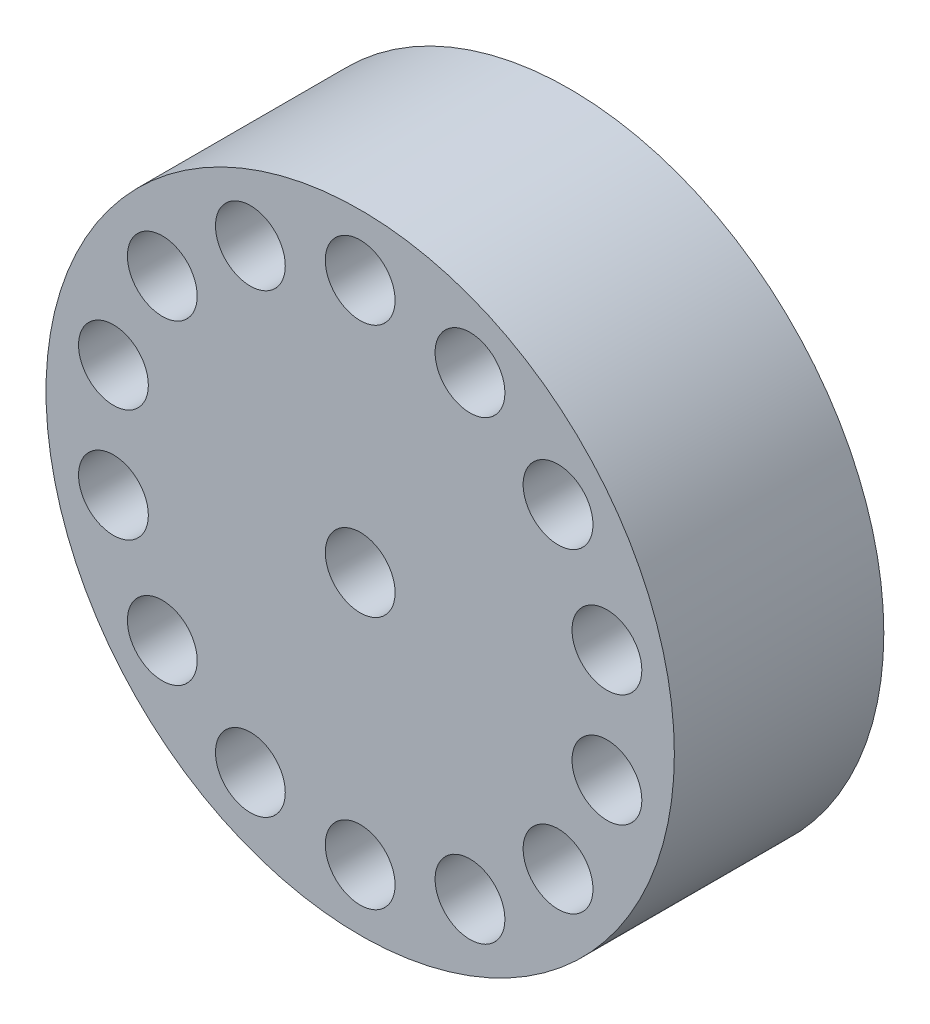
SolidWorks part; units mm, degrees
ref_plane "Płaszczyzna przednia" through (0, 0, 0) normal (0, 0, 1) x (1, 0, 0)
ref_plane "Płaszczyzna górna" through (0, 0, 0) normal (0, 1, 0) x (1, 0, 0)
ref_plane "Płaszczyzna prawa" through (0, 0, 0) normal (1, 0, 0) x (0, 0, -1)
sketch "Szkic1" plane through (0, 0, 0) normal (0, 0, 1) x (1, 0, 0)
  circle A0 centre (0, 0) radius 4.5
  circle A1 centre (0, 0) radius 0.5
extrude "Dodanie-wyciągnięcie1" add sketch "Szkic1" along normal blind 3
sketch "Szkic2" plane through (0, 0, 3) normal (0, 0, 1) x (1, 0, 0)
  circle A0 centre (0, 3.625) radius 0.5
  circle A1 centre (1.5728, 3.266) radius 0.5
  circle A2 centre (2.8341, 2.2602) radius 0.5
  circle A3 centre (3.5341, 0.8066) radius 0.5
  circle A4 centre (3.5341, -0.8066) radius 0.5
  circle A5 centre (2.8341, -2.2602) radius 0.5
  circle A6 centre (1.5728, -3.266) radius 0.5
  circle A7 centre (0, -3.625) radius 0.5
  circle A8 centre (-1.5728, -3.266) radius 0.5
  circle A9 centre (-2.8341, -2.2602) radius 0.5
  circle A10 centre (-3.5341, -0.8066) radius 0.5
  circle A11 centre (-3.5341, 0.8066) radius 0.5
  circle A12 centre (-2.8341, 2.2602) radius 0.5
  circle A13 centre (-1.5728, 3.266) radius 0.5
  point P31 (0, 0)
  dimension "D1" = 1
  dimension "D2" = 3.625
  dimension "D3" = 14
extrude "Wytnij-wyciągnięcie1" cut sketch "Szkic2" against normal blind 1
